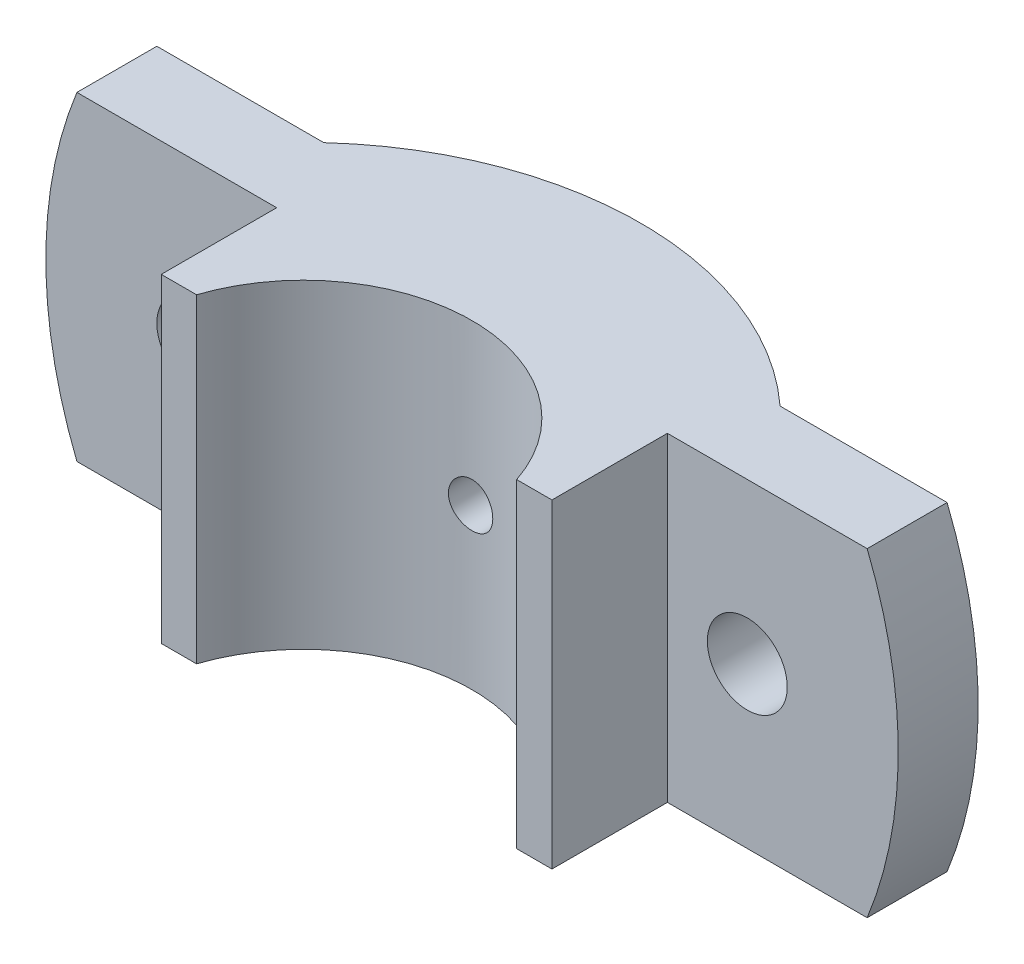
SolidWorks part; units mm, degrees
ref_plane "Front Plane" through (0, 0, 0) normal (0, 0, 1) x (1, 0, 0)
ref_plane "Top Plane" through (0, 0, 0) normal (0, 1, 0) x (1, 0, 0)
ref_plane "Right Plane" through (0, 0, 0) normal (1, 0, 0) x (0, 0, -1)
sketch "Sketch2" plane through (0, 0, 0) normal (0, 1, 0) x (1, 0, 0)
  line L0 (0, -16.0979) -> (0, 27.0716) construction
  line L1 (18.0278, 6) -> (22, 6)
  line L2 (22, 6) -> (22, 19)
  line L3 (22, 19) -> (50, 19)
  line L4 (50, 19) -> (50, 28)
  line L5 (50, 28) -> (25.6905, 28)
  line L6 (-50, 28) -> (-25.6905, 28)
  line L7 (-50, 19) -> (-50, 28)
  line L8 (-22, 19) -> (-50, 19)
  line L9 (-22, 6) -> (-22, 19)
  line L10 (-18.0278, 6) -> (-22, 6)
  arc A0 (-18.0278, 6) -> (18.0278, 6) centre (0, 0) cw
  arc A1 (25.6905, 28) -> (-25.6905, 28) centre (0, 0) ccw
  dimension "D1" = 19
  dimension "D2" = 9
  dimension "D7" = 38
  dimension "D3" = 44
  dimension "D4" = 19
  dimension "D5" = 13
  dimension "D6" = 50
extrude "Boss-Extrude1" add sketch "Sketch2" along normal mid plane 36
sketch "Sketch3" plane through (0, 0, -28) normal (0, 0, -1) x (-1, 0, 0)
  line L0 (25.6905, 18) -> (-25.6905, 18) construction
  circle A0 centre (-31, 0) radius 4.5
  point P2 (0, 18)
  point P5 (0, 18)
  point P6 (0, 0)
  dimension "D1" = 31
  dimension "D2" = 9
extrude "Cut-Extrude1" cut sketch "Sketch3" against normal through all
mirror "Mirror1" about plane through (0, 0, 0) normal (1, 0, 0) of "Cut-Extrude1"
ref_plane "Plane1" through (0, 0, -28) normal (0, 0, -1) x (-1, 0, 0)
sketch "Sketch4" plane through (0, 0, -28) normal (0, 0, -1) x (-1, 0, 0)
  line L0 (25.6905, 18) -> (25.6905, -18) construction
  line L2 (25.6905, 18) -> (25.6905, -18)
  line L4 (-22, 18) -> (-50, 18) construction
  line L5 (-22, -18) -> (-50, -18) construction
  line L6 (-50, 18) -> (-50, -18) construction
  line L7 (50, -18) -> (22, -18) construction
  line L8 (50, 18) -> (50, -18) construction
  line L9 (50, 18) -> (22, 18) construction
  line L10 (-44.4972, 18) -> (-50, 18)
  line L11 (-44.4972, -18) -> (-50, -18)
  line L12 (-50, 18) -> (-50, -18)
  line L13 (50, -18) -> (44.4972, -18)
  line L14 (50, 18) -> (50, -18)
  line L15 (50, 18) -> (44.4972, 18)
  line L16 (25.6905, 18) -> (22, 18)
  line L17 (25.6905, -18) -> (22, -18)
  arc A1 (-44.4972, 18) -> (-44.4972, -18) centre (0, 0) ccw
  arc A2 (44.4972, -18) -> (44.4972, 18) centre (0, 0) ccw
  dimension "D2" = 96
extrude "Cut-Extrude5" cut sketch "Sketch4" against normal through all contours A2 L13 L14 L15 | A1 L10 L12 L11
hole_wizard "CBORE for M5 Hex Head Bolt5" positions "3DSketch7" profile "Sketch10" counterbore size "M5" standard "ANSI Metric" end condition through all
sketch3d "3DSketch7"
  point P0 (0, 0, -38)
  dimension "D1" = 0
  dimension "D2" = 0
sketch "Sketch10" plane through (0, 0, -38) normal (1, 0, 0) x (0, 1, 0)
  line L0 (0, 0) -> (0, 32)
  line L1 (0, 32) -> (2.5, 32)
  line L2 (2.5, 13.3001) -> (2.5, 32)
  line L3 (2.5, 13.3001) -> (2.9995, 13)
  line L4 (2.9995, 13) -> (3, 13)
  line L5 (3, 13) -> (3, 0)
  line L7 (0, 0) -> (3, 0)
  line L9 (-2.5, 13.3001) -> (-2.9995, 13) construction
  line L11 (0, -6.35) -> (0, 107.95) construction
  dimension "Thru Hole Dia." = 5
  dimension "Thru Hole Depth" = 32
  dimension "C'Bore Dia." = 6
  dimension "C'Bore Depth" = 13
  dimension "Mid C'Sink Dia." = 5.999
  dimension "Mid C'Sink Angle" = 118
sketch "Sketch11" plane through (0, 0, -28) normal (0, 0, -1) x (-1, 0, 0)
  line L0 (25.6905, 18) -> (25.6905, -18) construction
  line L1 (25.6905, 6.6377) -> (25.6905, -6.6377)
  arc A0 (25.6905, 6.6377) -> (25.6905, -6.6377) centre (31, 0) ccw
  dimension "D1" = 17
extrude "Cut-Extrude10" cut sketch "Sketch11" along normal up to surface up to face at (2.922, 0.6795, -37.8875)
mirror "Mirror2" about plane through (0, 0, 0) normal (1, 0, 0) of "Cut-Extrude10"
